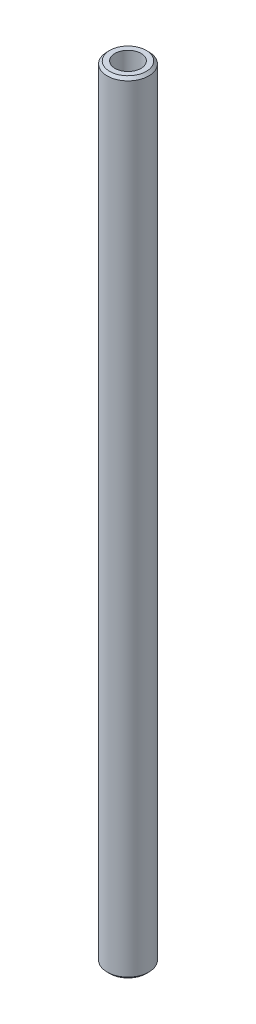
SolidWorks part; units mm, degrees
ref_plane "Face" through (0, 0, 0) normal (0, 0, 1) x (1, 0, 0)
ref_plane "Dessus" through (0, 0, 0) normal (0, 1, 0) x (1, 0, 0)
ref_plane "Droite" through (0, 0, 0) normal (1, 0, 0) x (0, 0, -1)
sketch "Esquisse1" plane through (0, 0, 0) normal (0, 1, 0) x (1, 0, 0)
  circle A0 centre (0, 0) radius 4
  dimension "D1" = 8
extrude "Extrusion1" add sketch "Esquisse1" along normal blind 150
chamfer "Chanfrein1" distance 0.5 angle 45 2 edges at (0, 150, 4) (0, 0, 4)
sketch "Esquisse2" plane through (0, 0, 0) normal (0, -1, 0) x (1, 0, 0)
  circle A0 centre (0, 0) radius 2.5
  dimension "D1" = 5
extrude "Extrusion2" cut sketch "Esquisse2" against normal blind 15
sketch "Esquisse3" plane through (0, 150, 0) normal (0, 1, 0) x (1, 0, 0)
  circle A0 centre (0, 0) radius 2.5
  dimension "D1" = 5
extrude "Extrusion3" cut sketch "Esquisse3" against normal blind 15
